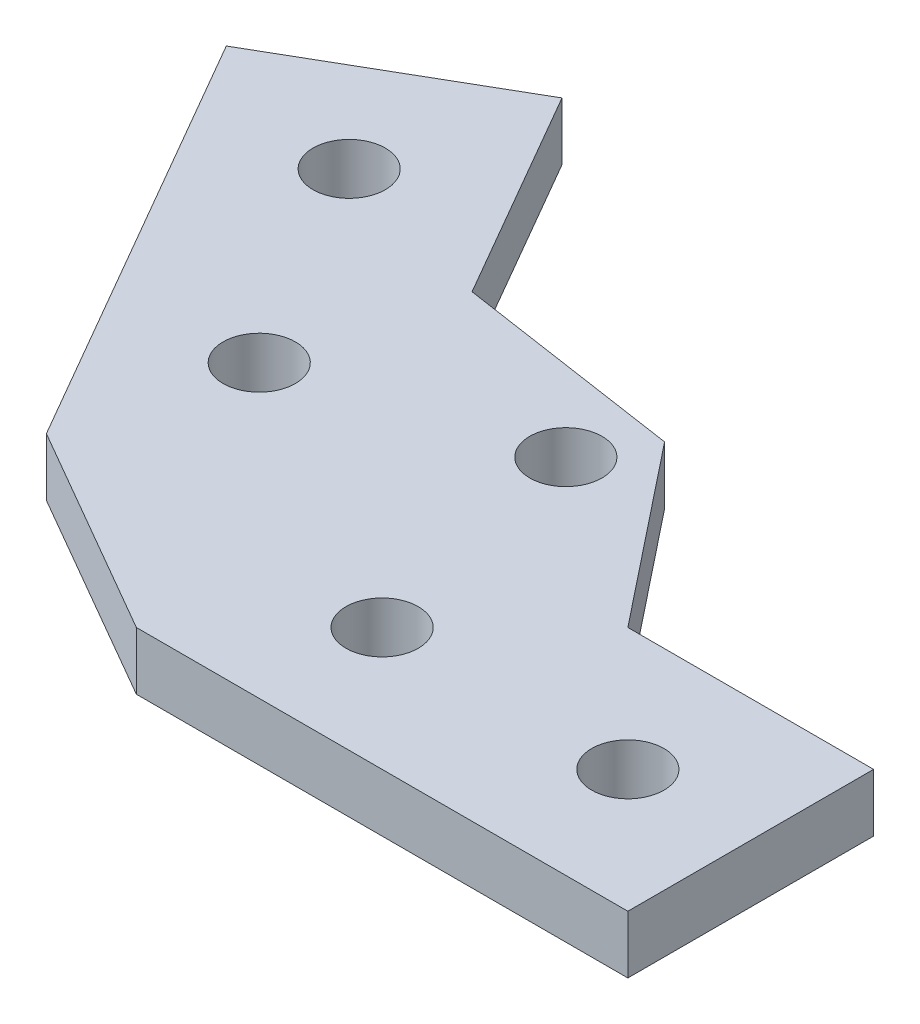
SolidWorks part; units mm, degrees
ref_plane "Front Plane" through (0, 0, 0) normal (0, 0, 1) x (1, 0, 0)
ref_plane "Top Plane" through (0, 0, 0) normal (0, 1, 0) x (1, 0, 0)
ref_plane "Right Plane" through (0, 0, 0) normal (1, 0, 0) x (0, 0, -1)
other "Configuration Table"
sketch "sketch1" plane through (0, 0, 0) normal (0, 1, 0) x (1, 0, 0)
  line L0 (0, -8.5) -> (8.5, -8.5) construction
  line L1 (0, 0) -> (34, 0)
  line L2 (0, 0) -> (0, -17)
  line L3 (0, -17) -> (34, -17)
  line L4 (34, 0) -> (34, -17)
  line L5 (8.5, -8.5) -> (25.5, -8.5) construction
  circle A1 centre (8.5, -8.5) radius 2.5
  circle A2 centre (25.5, -8.5) radius 2.5
  dimension "D4" = 5
  dimension "D1" = 17
  dimension "D2" = 34
  dimension "D3" = 8.5
  dimension "D6" = 17
  dimension "D5" = 2
extrude "Boss-Extrude1" add sketch "sketch1" along normal blind 4
sketch "Sketch9" plane through (0, 0, 0) normal (0, 1, 0) x (1, 0, 0)
  line L0 (0, 0) -> (34, 0) construction
  line L1 (0, 0) -> (17, 29.4449) construction
  dimension "D1" = 60
ref_plane "Plane2" through (0, 0, 0) normal (-0.866, 0, -0.5) x (-0.5, 0, 0.866)
mirror "Mirror6" about plane through (0, 0, 0) normal (-0.866, 0, -0.5) of bodies 102 110
sketch "Sketch11" plane through (0, 0, 0) normal (0, 1, 0) x (1, 0, 0)
  line L0 (-14.7224, -8.5) -> (0, -17)
  line L1 (0, 0) -> (-14.7224, -8.5) construction
  line L2 (0, 0) -> (0, -17) construction
  line L3 (0, 0) -> (-14.7224, -8.5)
  line L4 (0, 0) -> (0, -17)
extrude "Boss-Extrude2" add sketch "Sketch11" along normal blind 4
sketch "Sketch13" plane through (0, 0, 0) normal (0, 1, 0) x (1, 0, 0)
  line L0 (-11.6112, 3.1112) -> (4.6528, 8.059) construction
  line L1 (0, 0) -> (17, 29.4449) construction
  line L2 (4.6528, 8.059) -> (8.5, -8.5) construction
  line L4 (7.1528, 12.3891) -> (-8.5, 14.7224)
  line L5 (-17, 29.4449) -> (0, 0) construction
  line L6 (7.1528, 12.3891) -> (17, 0)
  line L7 (0, 0) -> (34, 0) construction
  line L8 (0, 0) -> (17, 29.4449) construction
  line L9 (-8.5, 14.7224) -> (0, 0)
  line L10 (0, 0) -> (17, 0)
  circle A0 centre (8.5, -8.5) radius 2.5 construction
  circle A1 centre (-11.6112, 3.1112) radius 2.5 construction
  circle A2 centre (8.5, -8.5) radius 2.5 construction
  circle A3 centre (-11.6112, 3.1112) radius 2.5 construction
  circle A4 centre (4.6528, 8.059) radius 2.5
  dimension "D1" = 17
  dimension "D2" = 5
  dimension "D3" = 5
  dimension "D4" = 17
extrude "Boss-Extrude3" add sketch "Sketch13" along normal blind 4
equation "\"D2@sketch1\" = \"length\""
equation "\"holes\"= 2'Holes per side"
equation "\"cdist\"= 17mm'centre distance between holes"
equation "\"width\"= 17mm"
equation "\"length\"= \"cdist\" * \"holes\""
equation "\"D1@sketch1\"=\"width\""
equation "\"hdiam\"= 5mm'Hole diametre"
equation "\"D4@sketch1\" = \"hdiam\""
equation "\"D6@sketch1\" = \"cdist\""
equation "\"D5@sketch1\" = \"holes\""
equation "\"D1@Boss-Extrude1\"=\"supportheight\""
equation "\"joint\"= 120"
equation "\"D1@Sketch9\"=\"joint\"/2"
equation "\"D1@Boss-Extrude2\"=\"supportheight\""
equation "\"D2@Sketch13\"=\"hdiam\""
equation "\"D4@Sketch13\"=\"cdist\""
equation "\"D1@Boss-Extrude3\"=\"supportheight\""
equation "\"supportheight\"= 4mm"
equation "\"tolerance\"= 0.04mm"
equation "\"insetwidth\"= 7mm"
